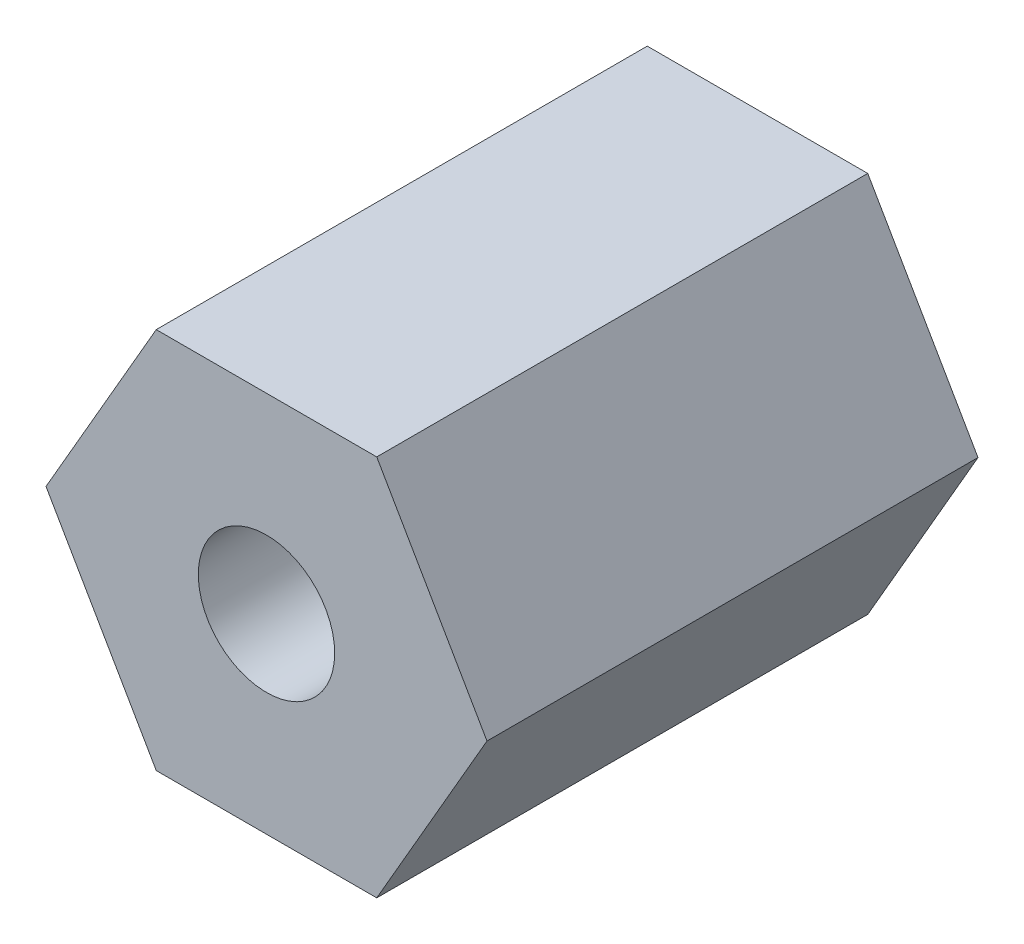
SolidWorks part; units mm, degrees
material "黃銅"
ref_plane "前基準面" through (0, 0, 0) normal (0, 0, 1) x (1, 0, 0)
ref_plane "上基準面" through (0, 0, 0) normal (0, 1, 0) x (1, 0, 0)
ref_plane "右基準面" through (0, 0, 0) normal (1, 0, 0) x (0, 0, -1)
sketch "草圖1" plane through (0, 0, 0) normal (0, 0, 1) x (1, 0, 0)
  line L1 (-2.0207, 3.5) -> (-4.0415, 0)
  line L2 (-4.0415, 0) -> (-2.0207, -3.5)
  line L3 (-2.0207, -3.5) -> (2.0207, -3.5)
  line L4 (2.0207, -3.5) -> (4.0415, 0)
  line L5 (4.0415, 0) -> (2.0207, 3.5)
  line L6 (2.0207, 3.5) -> (-2.0207, 3.5)
  circle A0 centre (0, 0) radius 3.5 construction
  dimension "D1" = 7
extrude "填料-伸長1" add sketch "草圖1" along normal blind 9
hole_wizard "M3x0.5 螺紋孔1" positions "草圖2" profile "草圖3" tap size "M3x0.5" standard "Ansi Metric" end condition through all
sketch "草圖2" plane through (0, 0, 9) normal (0, 0, 1) x (1, 0, 0)
  point P0 (0, 0)
sketch "草圖3" plane through (0, 0, 9) normal (1, 0, 0) x (0, -1, 0)
  line L0 (0, 0) -> (0, 9)
  line L1 (0, 9) -> (1.25, 9)
  line L2 (1.25, 9) -> (1.25, 0)
  line L5 (1.25, 0) -> (0, 0)
  line L11 (0, -6.35) -> (0, 107.95) construction
  dimension "貫穿螺孔鑽直徑" = 2.5
  dimension "貫穿螺孔鑽深度" = 9
